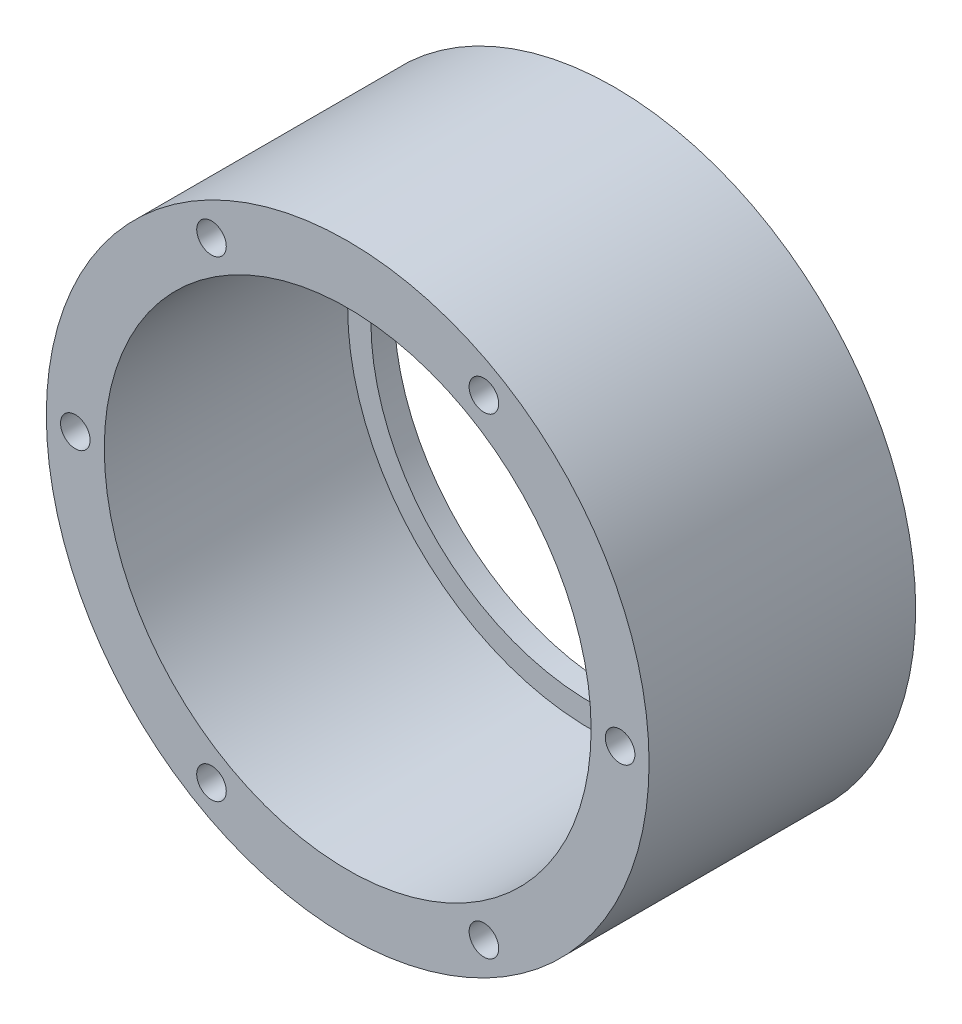
SolidWorks part; units mm, degrees
material "1060 Сплав"
ref_plane "Спереди" through (0, 0, 0) normal (0, 0, 1) x (1, 0, 0)
ref_plane "Сверху" through (0, 0, 0) normal (0, 1, 0) x (1, 0, 0)
ref_plane "Справа" through (0, 0, 0) normal (1, 0, 0) x (0, 0, -1)
sketch "Эскиз1" plane through (0, 0, 0) normal (1, 0, 0) x (0, 0, -1)
  line L3 (0, 26) -> (23, 26)
  line L4 (23, 26) -> (23, 19)
  line L6 (23, 19) -> (21, 19)
  line L7 (21, 19) -> (21, 21)
  line L8 (21, 21) -> (0, 21)
  line L9 (0, 0) -> (56.4457, 0) construction
  line L10 (0, 21) -> (0, 26)
  dimension "D1" = 42
  dimension "D2" = 38
  dimension "D3" = 52
  dimension "D4" = 2
  dimension "D5" = 23
revolve "Повернуть1" add sketch "Эскиз1" angle 360 about L9
hole_wizard "Сверло под метчик  спиральное M2.51" positions "Эскиз2" profile "Эскиз3" hole size "M2.5x0.45" standard "DIN"
sketch "Эскиз2" plane through (0, 0, 0) normal (0, 0, 1) x (1, 0, 0)
  point P0 (23.5, 0)
  dimension "D1" = 23.5
sketch "Эскиз3" plane through (23.5, 0, 0) normal (1, 0, 0) x (0, -1, 0)
  line L0 (0, 0) -> (0, 8.7661)
  line L1 (0, 8.7661) -> (1.275, 8)
  line L2 (1.275, 8) -> (1.275, 0)
  line L5 (1.275, 0) -> (0, 0)
  line L10 (0, 8.7661) -> (-1.275, 8) construction
  line L11 (0, -6.35) -> (0, 107.95) construction
  dimension "Диаметр отверстия" = 2.55
  dimension "Глубина отверстия" = 8
  dimension "Угол заточки сверла" = 118
pattern_circular "Круговой массив1" count 6 over 360 about axis through (0, 0, 0) along (0, 0, 1) of "Сверло под метчик  спиральное M2.51"
